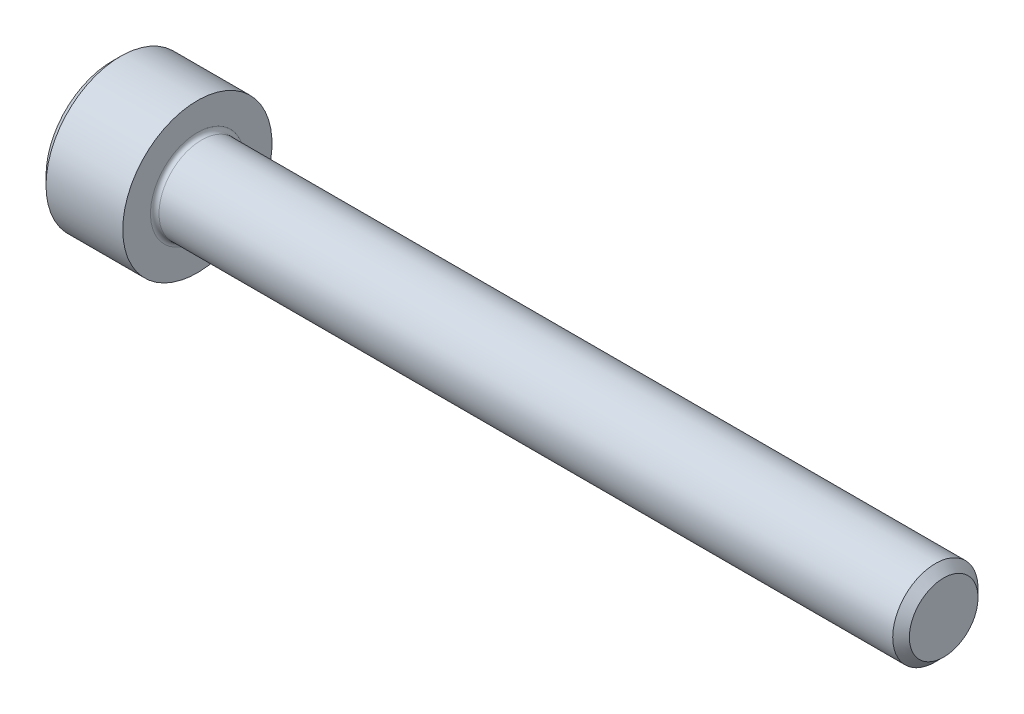
SolidWorks part; units mm, degrees
revolve "Base-Revolve" add sketch "BodySke"
sketch "BodySke" plane through (0, 0, 0) normal (0, 0, 1) x (1, 0, 0)
  line L0 (0, 0) -> (0, 3.1)
  line L1 (0.4, 3.5) -> (4, 3.5)
  line L2 (4, 3.5) -> (4, 2)
  line L3 (4, 2) -> (38.61, 2)
  line L4 (39, 1.61) -> (39, 0)
  line L5 (39, 0) -> (0, 0)
  line L6 (-31.75, 0) -> (127, 0) construction
  line L7 (0, 3.1) -> (0.4, 3.5)
  line L8 (39, 1.61) -> (38.61, 2)
  line L9 (0, -3.1) -> (0.4, -3.5) construction
  line L10 (39, -1.61) -> (38.61, -2) construction
  line L11 (4.7, 9.525) -> (4.7, 3.175) construction
  line L12 (19, 9.525) -> (19, 3.175) construction
  line L13 (-11, 9.525) -> (-11, 3.175) construction
  dimension "Diameter" = 4
  dimension "Head_ht" = 4
  dimension "Length" = 35
  dimension "Body_ch_ang" = 45
  dimension "Head_dia" = 7
  dimension "Head_ch_ang" = 45
  dimension "Minor_dia" = 3.22
  dimension "Advance" = 0.7
  dimension "Thread_nom" = 20
  dimension "Thread_length" = 50
  dimension "Head_ch_ht" = 0.4
cosmetic thread "ThreadCosmetic" [suppressed]
fillet "Fillet1" radius 0.2 1 edges at (4, 0, 2)
ref_plane "Plane1" through (0, 0, 0) normal (0, 0, 1) x (1, 0, 0)
ref_plane "Plane2" through (0, 0, 0) normal (0, 1, 0) x (1, 0, 0)
ref_plane "Plane3" through (0, 0, 0) normal (1, 0, 0) x (0, 0, -1)
sketch "Sketch2" plane through (0, 0, 0) normal (0, 0, 1) x (1, 0, 0)
  line L0 (0, 1.5355) -> (2, 1.5355)
  line L1 (2, 1.5355) -> (2.8865, 0)
  line L2 (-31.75, 0) -> (127, 0) construction
  line L3 (2.8865, 0) -> (0, 0)
  line L4 (0, 0) -> (0, 1.5355)
  line L5 (0, 3.1) -> (0, -3.1) construction
  line L6 (0, 0) -> (47.625, 0) construction
  line L7 (4, -3.5) -> (4, 3.5) construction
  dimension "D2" = 60
revolve "Hex-PreBroach" cut sketch "Sketch2" angle 360 about L6
sketch "Sketch3" plane through (0, 0, 0) normal (-1, 0, 0) x (0, 0.5, 0.866)
  line L0 (0.8865, 1.5355) -> (-0.8865, 1.5355)
  line L1 (-0.8865, 1.5355) -> (-1.773, 0)
  line L2 (0.8865, 1.5355) -> (1.773, 0)
  line L3 (0.8865, -1.5355) -> (1.773, 0)
  line L4 (0.8865, -1.5355) -> (-0.8865, -1.5355)
  line L5 (-0.8865, -1.5355) -> (-1.773, 0)
extrude "Hex" cut sketch "Sketch3" against normal blind 2
sketch "Sketch4" plane through (0, 0, 0) normal (-1, 0, 0) x (0, 0, 1)
  line L0 (0, 0) -> (1.7399, 0)
  line L1 (0, 0) -> (6.1484, 3.5498) construction
  line L2 (0, 0) -> (0.8699, 1.5068)
  line L3 (1.4457, 0.3947) -> (1.6607, 0.5189)
  line L4 (1.0647, 1.0546) -> (1.2797, 1.1788)
  arc A0 (1.4457, 0.3947) -> (1.0647, 1.0546) centre (0, 0) ccw
  arc A1 (1.7399, 0) -> (1.6607, 0.5189) centre (0, 0) ccw
  arc A2 (0.8699, 1.5068) -> (1.2797, 1.1788) centre (0, 0) cw
  dimension "D1" = 30
  dimension "D2" = 60
extrude "Spline" [suppressed] cut sketch "Sketch4" against normal blind 2
pattern_circular "CirPattern1" [suppressed] count 6 every 60
sketch "Sketch5" plane through (0, 0, 0) normal (0, 0, 1) x (1, 0, 0)
  line L0 (-31.75, 0) -> (127, 0) construction
  line L2 (0, 3.1) -> (0, -3.1) construction
  circle A0 centre (1.6, 0) radius 0.675
  dimension "Drilled_hole_dia" = 1.35
  dimension "Drilled_hole_loc" = 1.6
extrude "Hole" [suppressed] cut sketch "Sketch5" against normal through all and the other way through all
pattern_circular "Drilled-4" [suppressed] count 2 every 60
pattern_circular "Drilled-6" [suppressed] count 3 every 60
sketch "ThdSchSke" plane through (0, 0, 0) normal (0, 0, 1) x (1, 0, 0)
  line L0 (19, -1.61) -> (18.7269, -2)
  line L1 (19, -1.61) -> (19.2731, -2)
  line L2 (19.2731, -2) -> (19.2731, -2.5)
  line L3 (-3.175, 0) -> (5.1513, 0) construction
  line L5 (19.2731, -2.5) -> (18.7269, -2.5)
  line L6 (18.7269, -2.5) -> (18.7269, -2)
  line L7 (0, 3.1) -> (0, -3.1) construction
revolve "ThreadSchematic" [suppressed] cut sketch "ThdSchSke" angle 360 about L3
pattern_linear "ThdSchPat" [suppressed]
equation "\"D2@Sketch3\" = \"Hex_size@Sketch3\" / 2"
equation "\"D1@Sketch3\" = \"Hex_size@Sketch3\" / 2"
equation "\"D1@Sketch2\" = \"Hex_size@Sketch3\" / 2"
equation "\"D3@Sketch4\" = \"Spline_p_dim@Sketch4\" / 2"
equation "\"Thread_minor@ThreadCosmetic\"  =  \"Minor_dia@BodySke\""
equation "\"D2@CirPattern1\" = 360 / \"Num_teeth@CirPattern1\""
equation "\"Wall_thickness@Sketch2\" = \"Head_ht@BodySke\" - \"Key_eng@Hex\""
equation "\"Thread_length@ThreadCosmetic\" = ((sgn( (\"Length@BodySke\" - \"Advance@BodySke\" ) - \"Thread_nom@BodySke\" )-1)*( (\"Length@BodySke\" - \"Advance@BodySke\" ) - \"Thread_nom@BodySke\" ))/-2+ \"Thread_nom@BodySke\""
equation "\"Thread_minor@ThdSchSke\" = \"Minor_dia@BodySke\""
equation "\"Diameter@ThdSchSke\" = \"Diameter@BodySke\""
equation "\"Overcut@ThdSchSke\" = \"Diameter@BodySke\" * 1.25"
equation "\"Start@ThdSchSke\" = \"Head_ht@BodySke\" + \"Length@BodySke\" - \"Thread_length@ThreadCosmetic\"  '---Non-countersunk---"
equation "\"Num_threads@ThdSchPat\" = int( \"Thread_length@ThreadCosmetic\" / \"Advance@BodySke\" + 0.999 )  + 1"
equation "\"Advance@ThdSchPat\" = \"Thread_length@ThreadCosmetic\" /  (\"Num_threads@ThdSchPat\" - 1) 'relax it"
equation "\"Num_threads@ThdSchPat\" = \"Num_threads@ThdSchPat\" - sgn( \"Num_threads@ThdSchPat\" - 1) '---chamfered tips only---"
